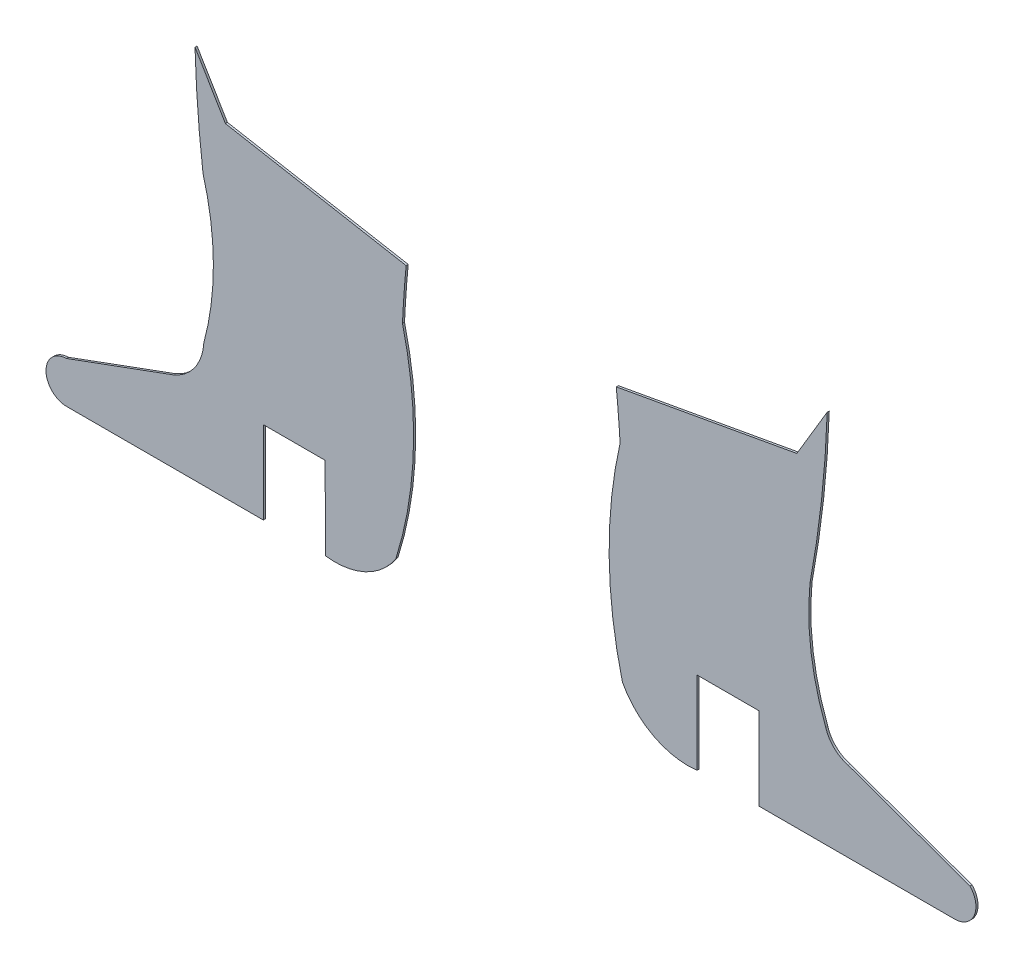
SolidWorks part; units mm, degrees
ref_plane "Alzado" through (0, 0, 0) normal (0, 0, 1) x (1, 0, 0)
ref_plane "Planta" through (0, 0, 0) normal (0, 1, 0) x (1, 0, 0)
ref_plane "Vista lateral" through (0, 0, 0) normal (1, 0, 0) x (0, 0, -1)
sketch "Model" plane through (0, 0, 0) normal (0, 0, 1) x (1, 0, 0)
  line L0 (26.5013, -36.0686) -> (26.5061, -40.0677)
  line L1 (23.5055, -36.069) -> (26.5013, -36.0686)
  line L2 (23.5061, -40.069) -> (23.5055, -36.069)
  line L3 (14.0073, -40.0704) -> (23.5061, -40.069)
  line L4 (19.1663, -36.1543) -> (13.9641, -38.0631)
  line L5 (57.7215, -38.3121) -> (51.8222, -36.1913)
  line L6 (47.5013, -40.0673) -> (57.0383, -40.0669)
  line L7 (47.5013, -36.0673) -> (47.5013, -40.0673)
  line L8 (44.5013, -36.0673) -> (47.5013, -36.0673)
  line L9 (44.5013, -40.0673) -> (44.5013, -36.0673)
  line L10 (50.8066, -21.8958) -> (49.3374, -24.3608)
  line L11 (49.3374, -24.3608) -> (40.5942, -25.9401)
  line L12 (20.1969, -21.8973) -> (21.6663, -24.3622)
  line L13 (21.6663, -24.3622) -> (30.4186, -25.9415)
  arc A0 (40.7792, -28.2089) -> (40.8903, -38.1684) centre (61.6733, -32.9562) ccw
  arc A1 (29.921, -38.4817) -> (30.2408, -28.4571) centre (12.2605, -32.9009) ccw
  arc A2 (26.5061, -40.0677) -> (29.921, -38.4817) centre (26.9668, -36.5903) ccw
  arc A3 (40.7792, -28.2089) -> (40.5942, -25.9401) centre (-17.4188, -31.8121) ccw
  arc A4 (13.9641, -38.0631) -> (14.0073, -40.0704) centre (13.9857, -39.0668) ccw
  arc A5 (30.4186, -25.9415) -> (30.2408, -28.4571) centre (83.6487, -30.9691) ccw
  arc A6 (20.1969, -21.8973) -> (20.5846, -26.9995) centre (74.3235, -20.3495) ccw
  arc A7 (19.1663, -36.1543) -> (20.6216, -34.0895) centre (18.2302, -33.9493) ccw
  arc A8 (20.6216, -34.0895) -> (20.5846, -26.9995) centre (7.8418, -30.611) ccw
  arc A9 (49.9719, -29.4875) -> (50.8066, -21.8958) centre (0.7668, -20.2357) ccw
  arc A10 (49.9719, -29.4875) -> (50.7353, -35.1506) centre (62.3702, -30.6992) ccw
  arc A11 (50.7353, -35.1506) -> (51.8222, -36.1913) centre (52.2033, -34.7054) ccw
  arc A12 (57.0383, -40.0669) -> (57.7215, -38.3121) centre (56.9696, -39.0297) ccw
  arc A13 (40.8903, -38.1684) -> (44.5013, -40.0673) centre (44.0753, -36.4946) ccw
extrude "Saliente-Extruir1" add sketch "Model" along normal blind 0.1
